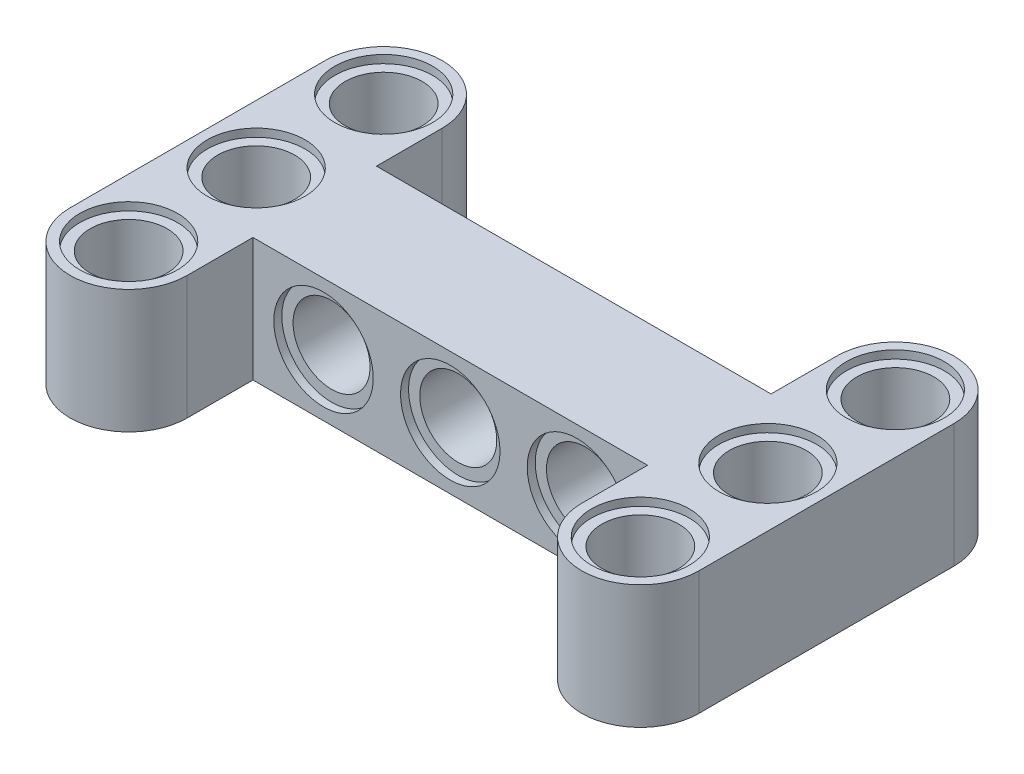
SolidWorks part; units mm, degrees
ref_plane "Front Plane" through (0, 0, 0) normal (0, 0, 1) x (1, 0, 0)
ref_plane "Top Plane" through (0, 0, 0) normal (0, 1, 0) x (1, 0, 0)
ref_plane "Right Plane" through (0, 0, 0) normal (1, 0, 0) x (0, 0, -1)
sketch "Sketch1" plane through (0, 0, 0) normal (0, 1, 0) x (1, 0, 0)
  line L0 (15.95, 4.1) -> (15.95, -11.8) construction
  line L5 (19.6, 4.1) -> (19.6, -11.8)
  line L6 (12.3, 4.1) -> (12.3, 0)
  line L7 (-987.7, -3.85) -> (49012.3, -3.85) construction
  line L8 (0, -12.76) -> (0, 12.76) construction
  line L9 (-12.3, -7.7) -> (12.3, -7.7)
  line L11 (-12.3, 0) -> (12.3, 0)
  line L13 (-12.3, -7.7) -> (12.3, 0) construction
  line L14 (-12.3, 0) -> (12.3, -7.7) construction
  line L15 (15.95, -997.6789) -> (15.95, 49002.3211) construction
  line L16 (-15.95, 4.1) -> (-15.95, -11.8) construction
  line L17 (-19.6, 4.1) -> (-19.6, -11.8)
  line L18 (-12.3, 4.1) -> (-12.3, 0)
  line L19 (12.3, -7.7) -> (12.3, -11.8)
  line L20 (-12.3, -7.7) -> (-12.3, -11.8)
  arc A0 (19.6, 4.1) -> (12.3, 4.1) centre (15.95, 4.1) ccw
  arc A1 (12.3, -11.8) -> (19.6, -11.8) centre (15.95, -11.8) ccw
  circle A2 centre (15.95, 4.1) radius 2.4
  circle A3 centre (15.95, 4.1) radius 3.05 construction
  circle A12 centre (15.95, -3.85) radius 3.05 construction
  circle A13 centre (15.95, -3.85) radius 2.4
  circle A14 centre (15.95, -11.8) radius 3.05 construction
  circle A15 centre (15.95, -11.8) radius 2.4
  arc A16 (-19.6, 4.1) -> (-12.3, 4.1) centre (-15.95, 4.1) cw
  arc A17 (-12.3, -11.8) -> (-19.6, -11.8) centre (-15.95, -11.8) cw
  circle A18 centre (-15.95, -11.8) radius 2.4
  circle A19 centre (-15.95, -11.8) radius 3.05 construction
  circle A20 centre (-15.95, -3.85) radius 2.4
  circle A21 centre (-15.95, -3.85) radius 3.05 construction
  circle A22 centre (-15.95, 4.1) radius 3.05 construction
  circle A23 centre (-15.95, 4.1) radius 2.4
  point P0 (0, -3.85)
  point P7 (15.95, -3.85)
  point P16 (15.95, 7.75)
  point P17 (15.95, -15.45)
  point P22 (0, -21.4827)
  point P27 (-15.95, -3.85)
  point P46 (0, -3.85)
  point P47 (0, -17.3698)
  point P48 (0, -3.85)
  dimension "D6" = 6.1
  dimension "D7" = 4.8
  dimension "D12" = 3
  dimension "D1" = 24.6
  dimension "D2" = 7.7
  dimension "D3" = 7.3
  dimension "D4" = 23.2
extrude "Boss-Extrude2" add sketch "Sketch1" along normal blind 7.7
sketch "Sketch2" plane through (0, 7.7, 0) normal (0, 1, 0) x (1, 0, 0)
  line L0 (0, -1000) -> (0, 49000) construction
  circle A0 centre (15.95, 4.1) radius 3.05
  circle A1 centre (15.95, -3.85) radius 3.05
  circle A2 centre (15.95, -11.8) radius 3.05
  circle A3 centre (15.95, 4.1) radius 2.4
  circle A4 centre (15.95, -3.85) radius 2.4
  circle A5 centre (15.95, -11.8) radius 2.4
  circle A6 centre (-15.95, -11.8) radius 2.4
  circle A7 centre (-15.95, -3.85) radius 2.4
  circle A8 centre (-15.95, 4.1) radius 2.4
  circle A9 centre (-15.95, -11.8) radius 3.05
  circle A10 centre (-15.95, -3.85) radius 3.05
  circle A11 centre (-15.95, 4.1) radius 3.05
  circle M10 centre (-15.95, -3.85) radius 2.4
  circle M11 centre (15.95, -11.8) radius 2.4
  circle M12 centre (15.95, 4.1) radius 2.4
  circle M25 centre (15.95, -3.85) radius 2.4
  circle M26 centre (-15.95, -11.8) radius 2.4
  circle M27 centre (-15.95, 4.1) radius 2.4
extrude "Cut-Extrude3" cut sketch "Sketch2" against normal blind 0.5 contours A11 M27 | A10 M10 | A9 M26 | A1 M25 | A0 M12 | A2 M11
ref_plane "Plane1" through (0, 3.85, 0) normal (0, 1, 0) x (1, 0, 0)
sketch "Sketch3" plane through (0, 0, 0) normal (0, 0, -1) x (-1, 0, 0)
  line L0 (12.3, -995.4281) -> (12.3, 49004.5719) construction
  line L1 (-1019.6, 3.85) -> (48980.4, 3.85) construction
  line L2 (-12.3, -995.4747) -> (-12.3, 49004.5253) construction
  line L3 (-19.6, 7.7) -> (-19.6, 0) construction
  line L4 (10.3, -996.15) -> (10.3, 49003.85) construction
  line L5 (12.3, 7.7) -> (12.3, 0) construction
  line L6 (-12.3, 7.7) -> (-12.3, 0) construction
  line L7 (-10.3, -996.15) -> (-10.3, 49003.85) construction
  line L8 (0, -1000) -> (0, 49000) construction
  circle A0 centre (7.9, 3.85) radius 2.4
  circle A1 centre (0, 3.85) radius 2.4
  circle A2 centre (-7.9, 3.85) radius 2.4
  point P9 (-19.6, 3.85)
  dimension "D1" = 2
  dimension "D2" = 4.8
  dimension "D4" = 2
  dimension "D5" = 7.9
  dimension "D6" = 7.9
  dimension "D3" = 3
extrude "Cut-Extrude4" cut sketch "Sketch3" against normal through all
sketch "Sketch4" plane through (0, 0, 0) normal (0, 0, -1) x (-1, 0, 0)
  circle A0 centre (-7.9, 3.85) radius 3.1
  circle A1 centre (0, 3.85) radius 3.1
  circle A2 centre (7.9, 3.85) radius 3.1
  circle A3 centre (-7.9, 3.85) radius 2.4
  circle A4 centre (0, 3.85) radius 2.4
  circle A5 centre (7.9, 3.85) radius 2.4
  circle M3 centre (7.9, 3.85) radius 2.4
  circle M4 centre (0, 3.85) radius 2.4
  circle M5 centre (-7.9, 3.85) radius 2.4
extrude "Cut-Extrude6" cut sketch "Sketch4" against normal blind 0.5 contours A0 M5 | A1 M4 | A2 M3
ref_plane "Plane2" through (0, 0, 3.85) normal (0, 0, -1) x (-1, 0, 0)
mirror "Mirror1" about plane through (0, 0, 3.85) normal (0, 0, -1) of "Cut-Extrude6"
mirror "Mirror2" about plane through (0, 3.85, 0) normal (0, 1, 0) of "Cut-Extrude3"
